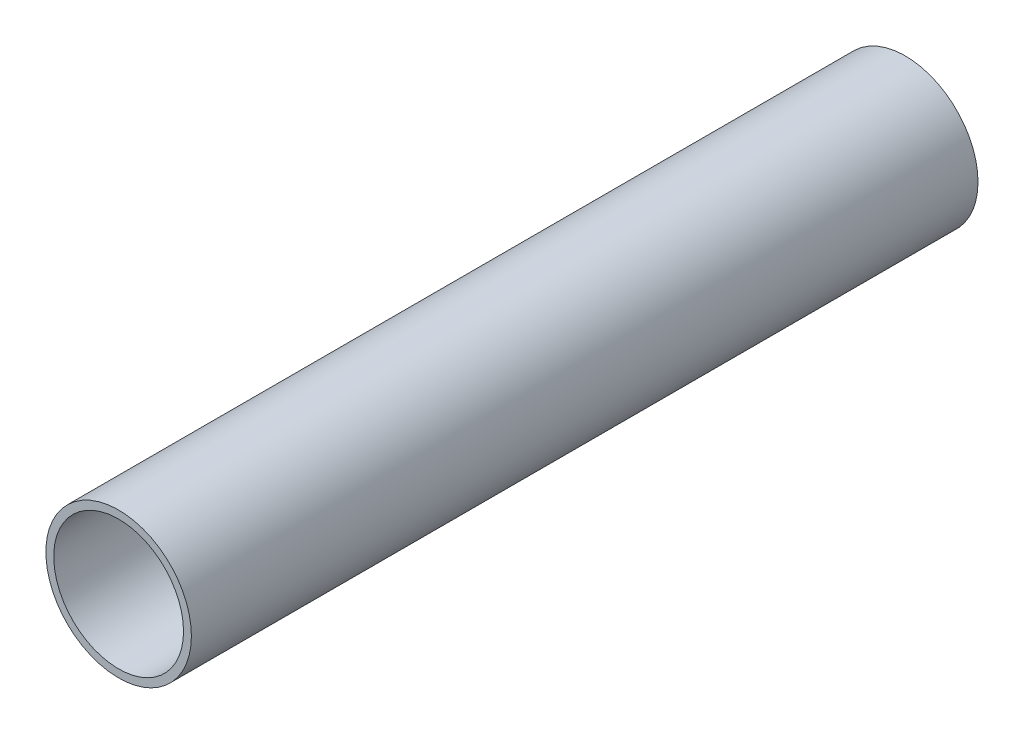
SolidWorks part; units mm, degrees
ref_plane "Front Plane" through (0, 0, 0) normal (0, 0, 1) x (1, 0, 0)
ref_plane "Top Plane" through (0, 0, 0) normal (0, 1, 0) x (1, 0, 0)
ref_plane "Right Plane" through (0, 0, 0) normal (1, 0, 0) x (0, 0, -1)
sketch "Sketch2" plane through (0, 0, 0) normal (0, 0, 1) x (1, 0, 0)
  circle A0 centre (0, 0) radius 23.495
  circle A1 centre (0, 0) radius 20.955
  dimension "D1" = 46.99
  dimension "D2" = 41.91
extrude "Boss-Extrude1" add sketch "Sketch2" against normal blind 254
